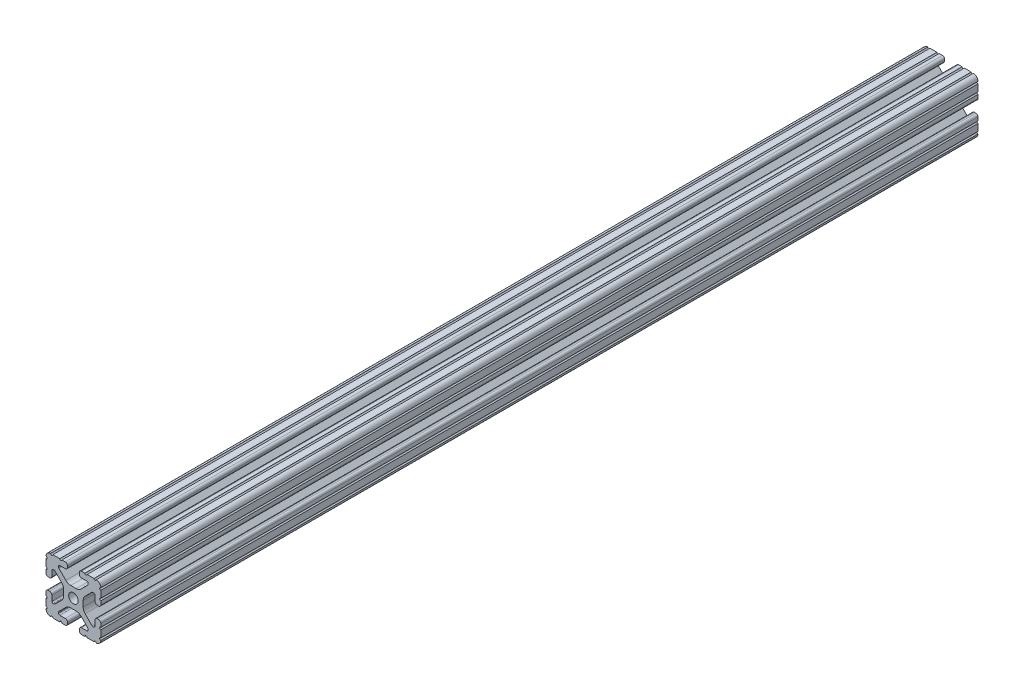
SolidWorks part; units mm, degrees
material "6061 Alloy"
ref_plane "Front Plane" through (0, 0, 0) normal (0, 0, 1) x (1, 0, 0)
ref_plane "Top Plane" through (0, 0, 0) normal (0, 1, 0) x (1, 0, 0)
ref_plane "Right Plane" through (0, 0, 0) normal (1, 0, 0) x (0, 0, -1)
sketch "Sketch1" plane through (0, 0, 0) normal (0, 0, 1) x (1, 0, 0)
  line L0 (0, 25.6181) -> (0, -24.623) construction
  line L1 (-20.8943, 0) -> (20.4607, 0) construction
  line L2 (-10.0229, 12.9148) -> (-5.2522, 8.144)
  line L3 (-10.287, 14.0843) -> (-10.287, 13.5524)
  line L4 (-5.6176, 14.986) -> (-9.3853, 14.986)
  line L5 (-4.064, 17.4964) -> (-4.064, 16.5396)
  line L6 (-7.9742, 19.05) -> (-5.6176, 19.05)
  line L7 (-14.3277, 19.05) -> (-9.4982, 19.05)
  line L8 (-19.05, 9.4961) -> (-19.05, 14.3277)
  line L9 (-19.05, 5.6176) -> (-19.05, 7.9763)
  line L10 (-16.5396, 4.064) -> (-17.4964, 4.064)
  line L11 (-14.986, 9.3853) -> (-14.986, 5.6176)
  line L12 (-13.516, 10.287) -> (-14.0843, 10.287)
  line L13 (-8.1476, 5.2921) -> (-12.8784, 10.0229)
  line L14 (-6.7564, -1.9335) -> (-6.7564, 1.9335)
  line L15 (-12.8784, -10.0229) -> (-8.1476, -5.2921)
  line L16 (-14.0843, -10.287) -> (-13.516, -10.287)
  line L17 (-14.986, -5.6176) -> (-14.986, -9.3853)
  line L18 (-17.4964, -4.064) -> (-16.5396, -4.064)
  line L19 (-19.05, -7.9763) -> (-19.05, -5.6176)
  line L20 (-19.05, -14.3277) -> (-19.05, -9.4961)
  line L21 (-9.4961, -19.05) -> (-14.3277, -19.05)
  line L22 (-5.6176, -19.05) -> (-7.9763, -19.05)
  line L23 (-4.064, -17.4964) -> (-4.064, -16.5396)
  line L24 (10.0229, -12.9148) -> (5.2522, -8.144)
  line L25 (10.287, -14.0843) -> (10.287, -13.5524)
  line L26 (5.6176, -14.986) -> (9.3853, -14.986)
  line L28 (-1.9022, 6.7564) -> (1.9022, 6.7564)
  line L29 (-1.9022, -6.7564) -> (1.9022, -6.7564)
  line L31 (-5.6176, -14.986) -> (-9.3853, -14.986)
  line L32 (-10.287, -14.0843) -> (-10.287, -13.5524)
  line L33 (-10.0229, -12.9148) -> (-5.2522, -8.144)
  line L66 (4.064, -16.5396) -> (4.064, -17.4964)
  line L67 (5.6176, -19.05) -> (7.9763, -19.05)
  line L68 (9.4961, -19.05) -> (14.3277, -19.05)
  line L69 (19.05, -14.3277) -> (19.05, -9.4961)
  line L70 (19.05, -7.9763) -> (19.05, -5.6176)
  line L71 (17.4964, -4.064) -> (16.5396, -4.064)
  line L72 (14.986, -5.6176) -> (14.986, -9.3853)
  line L73 (14.0843, -10.287) -> (13.516, -10.287)
  line L74 (12.8784, -10.0229) -> (8.1476, -5.2921)
  line L75 (6.7564, -1.9335) -> (6.7564, 1.9335)
  line L76 (8.1476, 5.2921) -> (12.8784, 10.0229)
  line L77 (13.516, 10.287) -> (14.0843, 10.287)
  line L78 (14.986, 9.3853) -> (14.986, 5.6176)
  line L79 (16.5396, 4.064) -> (17.4964, 4.064)
  line L80 (19.05, 5.6176) -> (19.05, 7.9763)
  line L81 (19.05, 9.4961) -> (19.05, 14.3277)
  line L82 (14.3277, 19.05) -> (9.4982, 19.05)
  line L83 (7.9742, 19.05) -> (5.6176, 19.05)
  line L84 (4.064, 17.4964) -> (4.064, 16.5396)
  line L85 (5.6176, 14.986) -> (9.3853, 14.986)
  line L86 (10.287, 14.0843) -> (10.287, 13.5524)
  line L87 (10.0229, 12.9148) -> (5.2522, 8.144)
  arc A0 (-10.0229, 12.9148) -> (-10.287, 13.5524) centre (-9.3853, 13.5524) cw
  circle A1 centre (0, 0) radius 3.3274
  arc A2 (-10.287, 14.0843) -> (-9.3853, 14.986) centre (-9.3853, 14.0843) cw
  arc A3 (-4.064, 16.5396) -> (-5.6176, 14.986) centre (-5.6176, 16.5396) cw
  arc A4 (-5.6176, 19.05) -> (-4.064, 17.4964) centre (-5.6176, 17.4964) cw
  arc A5 (-7.9742, 19.05) -> (-9.4982, 19.05) centre (-8.7362, 19.05) cw
  arc A6 (-14.3277, 19.05) -> (-15.8475, 19.05) centre (-15.0876, 18.9933) cw
  arc A7 (-19.05, 15.8475) -> (-15.8475, 19.05) centre (-15.8751, 15.8751) cw
  arc A8 (-19.05, 15.8475) -> (-19.05, 14.3277) centre (-18.9933, 15.0876) cw
  arc A9 (-19.05, 9.4961) -> (-19.05, 7.9763) centre (-18.9933, 8.7362) cw
  arc A10 (-17.4964, 4.064) -> (-19.05, 5.6176) centre (-17.4964, 5.6176) cw
  arc A11 (-14.986, 5.6176) -> (-16.5396, 4.064) centre (-16.5396, 5.6176) cw
  arc A12 (-14.986, 9.3853) -> (-14.0843, 10.287) centre (-14.0843, 9.3853) cw
  arc A13 (-13.516, 10.287) -> (-12.8784, 10.0229) centre (-13.516, 9.3853) cw
  arc A14 (-8.1476, 5.2921) -> (-6.7564, 1.9335) centre (-11.5062, 1.9335) cw
  arc A15 (-6.7564, -1.9335) -> (-8.1476, -5.2921) centre (-11.5062, -1.9335) cw
  arc A16 (-12.8784, -10.0229) -> (-13.516, -10.287) centre (-13.516, -9.3853) cw
  arc A17 (-14.0843, -10.287) -> (-14.986, -9.3853) centre (-14.0843, -9.3853) cw
  arc A18 (-16.5396, -4.064) -> (-14.986, -5.6176) centre (-16.5396, -5.6176) cw
  arc A19 (-19.05, -5.6176) -> (-17.4964, -4.064) centre (-17.4964, -5.6176) cw
  arc A20 (-19.05, -7.9763) -> (-19.05, -9.4961) centre (-18.9933, -8.7362) cw
  arc A21 (-19.05, -14.3277) -> (-19.05, -15.8475) centre (-18.9933, -15.0876) cw
  arc A22 (-15.8475, -19.05) -> (-19.05, -15.8475) centre (-15.8751, -15.8751) cw
  arc A23 (-15.8475, -19.05) -> (-14.3277, -19.05) centre (-15.0876, -18.9933) cw
  arc A24 (-9.4961, -19.05) -> (-7.9763, -19.05) centre (-8.7362, -18.9933) cw
  arc A25 (-4.064, -17.4964) -> (-5.6176, -19.05) centre (-5.6176, -17.4964) cw
  arc A26 (-5.2522, -8.144) -> (-1.9022, -6.7564) centre (-1.9022, -11.494) cw
  arc A27 (1.9022, -6.7564) -> (5.2522, -8.144) centre (1.9022, -11.494) cw
  arc A28 (10.0229, -12.9148) -> (10.287, -13.5524) centre (9.3853, -13.5524) cw
  arc A29 (10.287, -14.0843) -> (9.3853, -14.986) centre (9.3853, -14.0843) cw
  arc A30 (4.064, -16.5396) -> (5.6176, -14.986) centre (5.6176, -16.5396) cw
  arc A31 (-4.064, -16.5396) -> (-5.6176, -14.986) centre (-5.6176, -16.5396) ccw
  arc A32 (-10.287, -14.0843) -> (-9.3853, -14.986) centre (-9.3853, -14.0843) ccw
  arc A33 (-10.0229, -12.9148) -> (-10.287, -13.5524) centre (-9.3853, -13.5524) ccw
  arc A79 (4.064, -17.4964) -> (5.6176, -19.05) centre (5.6176, -17.4964) ccw
  arc A80 (9.4961, -19.05) -> (7.9763, -19.05) centre (8.7362, -18.9933) ccw
  arc A81 (15.8475, -19.05) -> (14.3277, -19.05) centre (15.0876, -18.9933) ccw
  arc A82 (15.8475, -19.05) -> (19.05, -15.8475) centre (15.8751, -15.8751) ccw
  arc A83 (19.05, -14.3277) -> (19.05, -15.8475) centre (18.9933, -15.0876) ccw
  arc A84 (19.05, -7.9763) -> (19.05, -9.4961) centre (18.9933, -8.7362) ccw
  arc A85 (19.05, -5.6176) -> (17.4964, -4.064) centre (17.4964, -5.6176) ccw
  arc A86 (16.5396, -4.064) -> (14.986, -5.6176) centre (16.5396, -5.6176) ccw
  arc A87 (14.0843, -10.287) -> (14.986, -9.3853) centre (14.0843, -9.3853) ccw
  arc A88 (12.8784, -10.0229) -> (13.516, -10.287) centre (13.516, -9.3853) ccw
  arc A89 (6.7564, -1.9335) -> (8.1476, -5.2921) centre (11.5062, -1.9335) ccw
  arc A90 (8.1476, 5.2921) -> (6.7564, 1.9335) centre (11.5062, 1.9335) ccw
  arc A91 (13.516, 10.287) -> (12.8784, 10.0229) centre (13.516, 9.3853) ccw
  arc A92 (14.986, 9.3853) -> (14.0843, 10.287) centre (14.0843, 9.3853) ccw
  arc A93 (14.986, 5.6176) -> (16.5396, 4.064) centre (16.5396, 5.6176) ccw
  arc A94 (17.4964, 4.064) -> (19.05, 5.6176) centre (17.4964, 5.6176) ccw
  arc A95 (19.05, 9.4961) -> (19.05, 7.9763) centre (18.9933, 8.7362) ccw
  arc A96 (19.05, 15.8475) -> (19.05, 14.3277) centre (18.9933, 15.0876) ccw
  arc A97 (19.05, 15.8475) -> (15.8475, 19.05) centre (15.8751, 15.8751) ccw
  arc A98 (14.3277, 19.05) -> (15.8475, 19.05) centre (15.0876, 18.9933) ccw
  arc A99 (7.9742, 19.05) -> (9.4982, 19.05) centre (8.7362, 19.05) ccw
  arc A100 (5.6176, 19.05) -> (4.064, 17.4964) centre (5.6176, 17.4964) ccw
  arc A101 (4.064, 16.5396) -> (5.6176, 14.986) centre (5.6176, 16.5396) ccw
  arc A102 (10.287, 14.0843) -> (9.3853, 14.986) centre (9.3853, 14.0843) ccw
  arc A103 (10.0229, 12.9148) -> (10.287, 13.5524) centre (9.3853, 13.5524) ccw
  arc A104 (1.9022, 6.7564) -> (5.2522, 8.144) centre (1.9022, 11.494) ccw
  arc A105 (-5.2522, 8.144) -> (-1.9022, 6.7564) centre (-1.9022, 11.494) ccw
  dimension "D1" = 6.6548
  dimension "D2" = 19.05
  dimension "D3" = 38.1
  dimension "D4" = 20.574
  dimension "D5" = 13.5128
  dimension "D6" = 4.064
  dimension "D7" = 8.128
  dimension "D8" = 4.064
  dimension "D9" = 12.2936
extrude "Extrude1" add sketch "Sketch1" against normal blind 609.6
